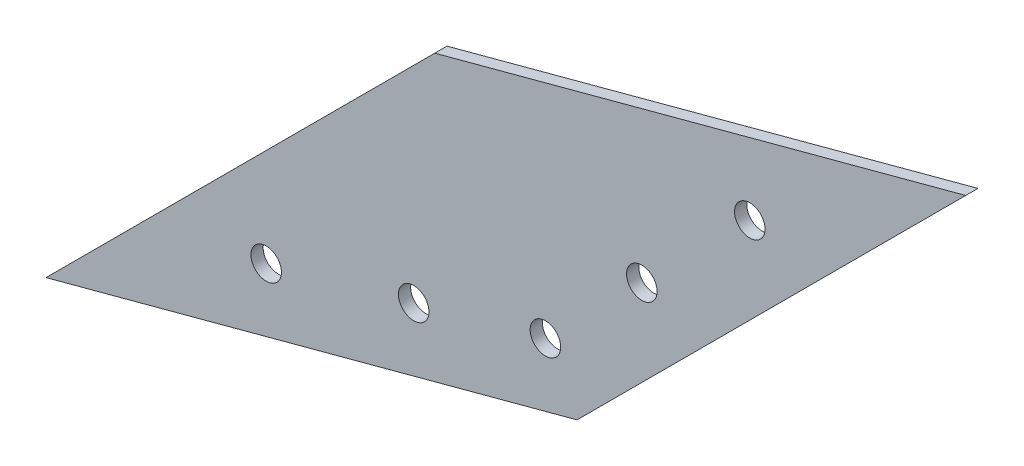
SolidWorks part; units mm, degrees
ref_plane "Front Plane" through (0, 0, 0) normal (0, 0, 1) x (1, 0, 0)
ref_plane "Top Plane" through (0, 0, 0) normal (0, 1, 0) x (1, 0, 0)
ref_plane "Right Plane" through (0, 0, 0) normal (1, 0, 0) x (0, 0, -1)
sketch "Sketch1" plane through (0, 0, 0) normal (0, 0, 1) x (1, 0, 0)
  line L0 (0, 0) -> (63.6396, 63.6396)
  line L1 (63.6396, 63.6396) -> (150.5729, 86.9333)
  line L2 (0, 0) -> (86.9333, 23.2937)
  line L3 (86.9333, 23.2937) -> (150.5729, 86.9333)
  dimension "D1" = 90
  dimension "D2" = 90
  dimension "D3" = 150
  dimension "D4" = 90
extrude "Boss-Extrude2" add sketch "Sketch1" along normal blind 2
sketch "Sketch7" plane through (0, 0, 2) normal (0, 0, 1) x (1, 0, 0)
  line L0 (86.9333, 23.2937) -> (122.2887, 58.6491)
  line L1 (86.9333, 23.2937) -> (150.5729, 86.9333) construction
  line L2 (122.2887, 58.6491) -> (115.2176, 65.7201)
  circle A0 centre (115.2176, 65.7201) radius 2.5
  dimension "D1" = 50
  dimension "D2" = 10
extrude "Cut-Extrude6" cut sketch "Sketch7" against normal blind 2 contours A0
sketch "Sketch8" plane through (0, 0, 2) normal (0, 0, 1) x (1, 0, 0)
  line L0 (86.9333, 23.2937) -> (104.611, 40.9714)
  line L1 (86.9333, 23.2937) -> (150.5729, 86.9333) construction
  line L2 (104.611, 40.9714) -> (97.5399, 48.0425)
  circle A0 centre (97.5399, 48.0425) radius 2.5
  dimension "D1" = 25
  dimension "D2" = 10
extrude "Cut-Extrude7" cut sketch "Sketch8" against normal blind 2
sketch "Sketch9" plane through (0, 0, 2) normal (0, 0, 1) x (1, 0, 0)
  line L0 (86.9333, 23.2937) -> (62.7852, 16.8232)
  line L1 (0, 0) -> (86.9333, 23.2937) construction
  line L2 (62.7852, 16.8232) -> (60.197, 26.4825)
  circle A0 centre (60.197, 26.4825) radius 2.5
  dimension "D1" = 25
  dimension "D2" = 90
  dimension "D3" = 10
extrude "Cut-Extrude8" cut sketch "Sketch9" against normal blind 2
sketch "Sketch10" plane through (0, 0, 2) normal (0, 0, 1) x (1, 0, 0)
  line L0 (86.9333, 23.2937) -> (38.637, 10.3528)
  line L1 (0, 0) -> (86.9333, 23.2937) construction
  line L2 (38.637, 10.3528) -> (36.0488, 20.012)
  circle A0 centre (36.0488, 20.012) radius 2.5
  dimension "D1" = 50
  dimension "D2" = 10
extrude "Cut-Extrude9" cut sketch "Sketch10" against normal blind 2
sketch "Sketch11" plane through (0, 0, 2) normal (0, 0, 1) x (1, 0, 0)
  line L0 (97.5399, 48.0425) -> (115.2176, 65.7201)
  line L1 (115.2176, 65.7201) -> (86.9333, 23.2937)
  line L2 (86.9333, 23.2937) -> (63.6396, 63.6396)
  line L3 (63.6396, 63.6396) -> (97.5399, 48.0425)
  line L4 (115.2176, 65.7201) -> (81.7569, 32.2595)
  circle A0 centre (81.7569, 32.2595) radius 2.5
extrude "Cut-Extrude10" cut sketch "Sketch11" against normal blind 2 contours L2 A0 | L2 A0 L4 | L4 A0 L2
